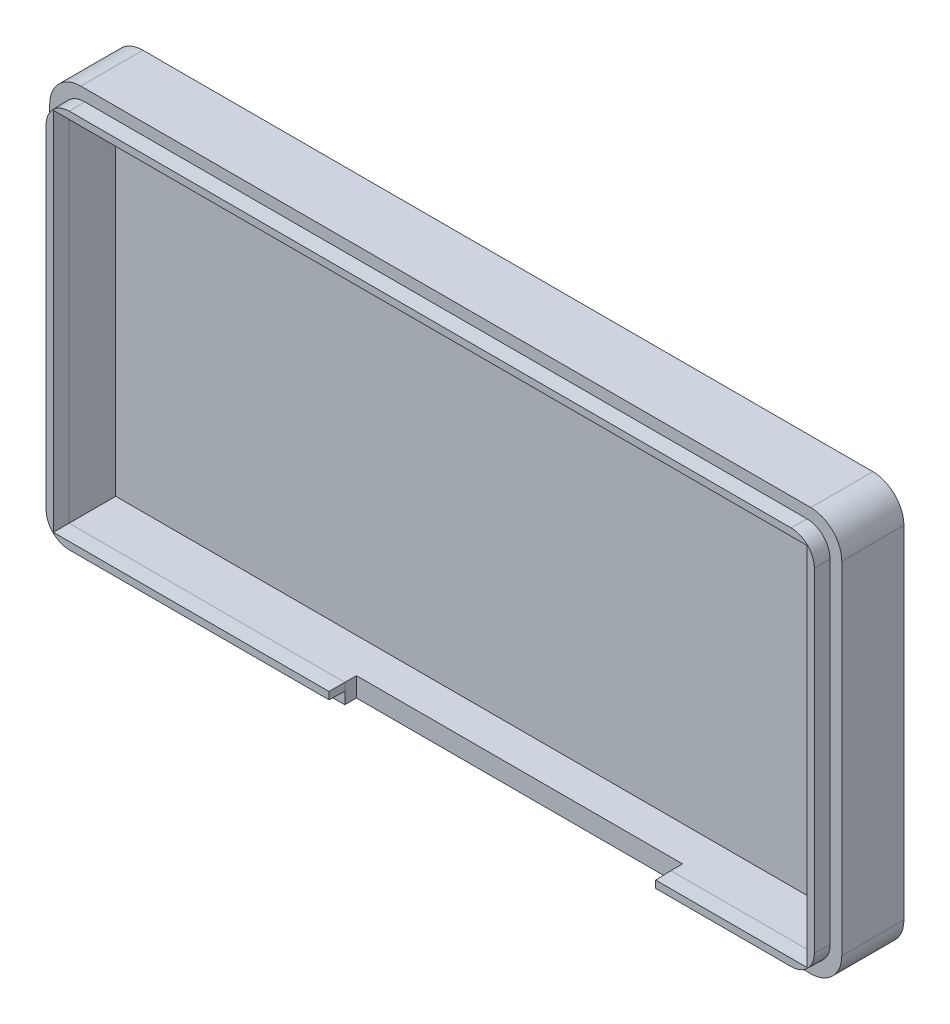
SolidWorks part; units mm, degrees
ref_plane "Front" through (0, 0, 0) normal (0, 0, 1) x (1, 0, 0)
ref_plane "Top" through (0, 0, 0) normal (0, 1, 0) x (1, 0, 0)
ref_plane "Right" through (0, 0, 0) normal (1, 0, 0) x (0, 0, -1)
sketch "Esquisse1" plane through (0, 0, 0) normal (0, 0, 1) x (1, 0, 0)
  line L1 (0, 0) -> (102, 0)
  line L2 (0, 0) -> (0, 52)
  line L3 (0, 52) -> (102, 52)
  line L4 (102, 0) -> (102, 52)
  dimension "D1" = 102
  dimension "D2" = 52
extrude "Boss.-Extru.1" add sketch "Esquisse1" along normal blind 2
sketch "Esquisse2" plane through (0, 0, 2) normal (0, 0, 1) x (1, 0, 0)
  line L4 (0, 52) -> (0, 0)
  line L5 (0, 0) -> (102, 0)
  line L6 (102, 0) -> (102, 52)
  line L7 (102, 52) -> (0, 52)
  line L8 (0, 52) -> (0, 0)
  line L9 (0, 0) -> (102, 0)
  line L10 (102, 0) -> (102, 52)
  line L11 (102, 52) -> (0, 52)
  dimension "D1" = 0
extrude "Extru.-Mince1" add sketch "Esquisse2" along normal blind 6 thin contours L8 L9 L10 L11 thin type one direction reverse wall 2.5
ref_plane "Plan1" through (0, 0, 8) normal (0, 0, 1) x (1, 0, 0)
sketch "Esquisse3" plane through (0, 0, 8) normal (0, 0, 1) x (1, 0, 0)
  line L1 (2.5, 49.5) -> (99.5, 49.5)
  line L2 (2.5, 49.5) -> (2.5, 2.5)
  line L3 (2.5, 2.5) -> (99.5, 2.5)
  line L4 (99.5, 49.5) -> (99.5, 2.5)
fillet "Congé2" radius 4 4 edges at (102, 52, 4) (0, 52, 4) (0, 0, 4) (102, 0, 4)
sketch "Esquisse4" plane through (0, 0, 0) normal (0, 1, 0) x (1, 0, 0)
  line L0 (98, -8) -> (4, -8) construction
  line L1 (80, -29.3244) -> (38, -29.3244)
  line L2 (80, -29.3244) -> (80, -6.5)
  line L3 (80, -6.5) -> (38, -6.5)
  line L4 (38, -29.3244) -> (38, -6.5)
  line L6 (102, -8) -> (102, 0) construction
  dimension "D1" = 42
  dimension "D2" = 1.5
  dimension "D3" = 22
extrude "Enlèv. mat.-Extru.1" cut sketch "Esquisse4" along normal blind 14
sketch "Esquisse5" plane through (0, 0, 8) normal (0, 0, 1) x (1, 0, 0)
  line L12 (99.5, 2.5) -> (80, 2.5)
  line L13 (80, 2.5) -> (80, 0)
  line L14 (80, 0) -> (98, 0)
  line L15 (102, 4) -> (102, 48)
  line L16 (98, 52) -> (4, 52)
  line L17 (0, 48) -> (0, 4)
  line L18 (4, 0) -> (38, 0)
  line L19 (38, 0) -> (38, 2.5)
  line L20 (38, 2.5) -> (2.5, 2.5)
  line L21 (2.5, 2.5) -> (2.5, 49.5)
  line L22 (2.5, 49.5) -> (99.5, 49.5)
  line L23 (99.5, 49.5) -> (99.5, 2.5)
  line L24 (99.5, 2.5) -> (80, 2.5)
  line L32 (38, 2.5) -> (2.5, 2.5)
  line L33 (2.5, 2.5) -> (2.5, 49.5)
  line L34 (2.5, 49.5) -> (99.5, 49.5)
  line L35 (99.5, 49.5) -> (99.5, 2.5)
  arc A4 (98, 0) -> (102, 4) centre (98, 4) ccw
  arc A5 (102, 48) -> (98, 52) centre (98, 48) ccw
  arc A6 (4, 52) -> (0, 48) centre (4, 48) ccw
  arc A7 (0, 4) -> (4, 0) centre (4, 4) ccw
  dimension "D1" = 0
extrude "Extru.-Mince2" add sketch "Esquisse5" along normal blind 2 draft 1 thin
fillet "Congé3" radius 3 4 edges at (1.5175, 1.5175, 9) (1.5175, 50.4825, 9) (100.4825, 50.4825, 9) (100.4825, 1.5175, 9)
